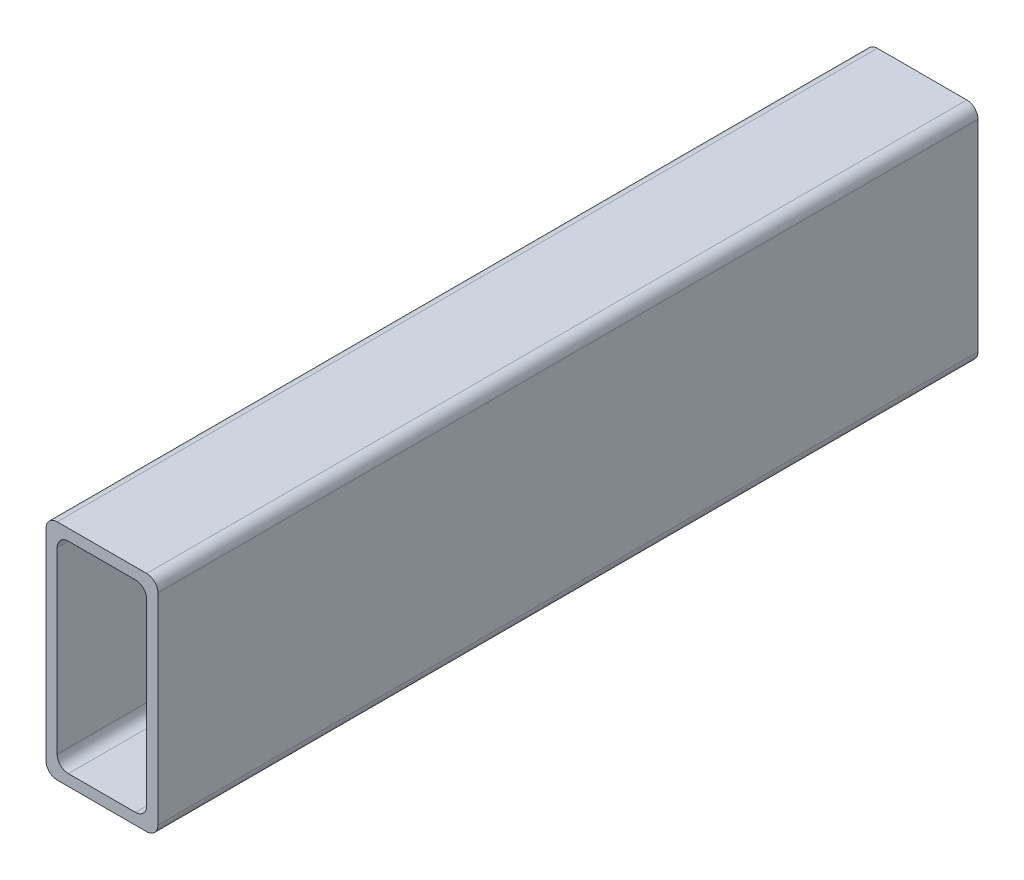
SolidWorks part; units mm, degrees
ref_plane "Płaszczyzna przednia" through (0, 0, 0) normal (0, 0, 1) x (1, 0, 0)
ref_plane "Płaszczyzna górna" through (0, 0, 0) normal (0, 1, 0) x (1, 0, 0)
ref_plane "Płaszczyzna prawa" through (0, 0, 0) normal (1, 0, 0) x (0, 0, -1)
sketch "Szkic1" plane through (0, 0, 0) normal (0, 0, 1) x (1, 0, 0)
  line L0 (-9, 27) -> (9, 27)
  line L1 (-12, -30) -> (12, -30)
  line L2 (-15, -27) -> (-15, 27)
  line L3 (-12, 30) -> (12, 30)
  line L4 (15, -27) -> (15, 27)
  line L5 (-15, -30) -> (15, 30) construction
  line L6 (-15, 30) -> (15, -30) construction
  line L7 (12, -24) -> (12, 24)
  line L8 (-9, -27) -> (9, -27)
  line L9 (-12, -24) -> (-12, 24)
  line L10 (-12, -27) -> (-12, 27) construction
  line L11 (-12, -27) -> (12, -27) construction
  line L12 (12, -27) -> (12, 27) construction
  line L13 (-12, 27) -> (12, 27) construction
  arc A0 (-15, 27) -> (-12, 30) centre (-12, 27) cw
  arc A1 (-12, -30) -> (-15, -27) centre (-12, -27) cw
  arc A2 (12, -30) -> (15, -27) centre (12, -27) ccw
  arc A3 (12, 30) -> (15, 27) centre (12, 27) cw
  arc A8 (-12, -24) -> (-9, -27) centre (-9, -24) ccw
  arc A9 (-12, -27) -> (-12, -27) centre (-12, -27) cw construction
  arc A10 (12, -24) -> (9, -27) centre (9, -24) cw
  arc A11 (12, -27) -> (12, -27) centre (12, -27) ccw construction
  arc A12 (-12, 24) -> (-9, 27) centre (-9, 24) cw
  arc A13 (-12, 27) -> (-12, 27) centre (-12, 27) cw construction
  arc A14 (9, 27) -> (12, 24) centre (9, 24) cw
  arc A15 (12, 27) -> (12, 27) centre (12, 27) cw construction
  point P0 (0, 0)
  dimension "D3" = 3
  dimension "D5" = 3
  dimension "D1" = 30
  dimension "D2" = 60
  dimension "D4" = 3
extrude "Dodanie-wyciągnięcie1" add sketch "Szkic1" along normal blind 220
